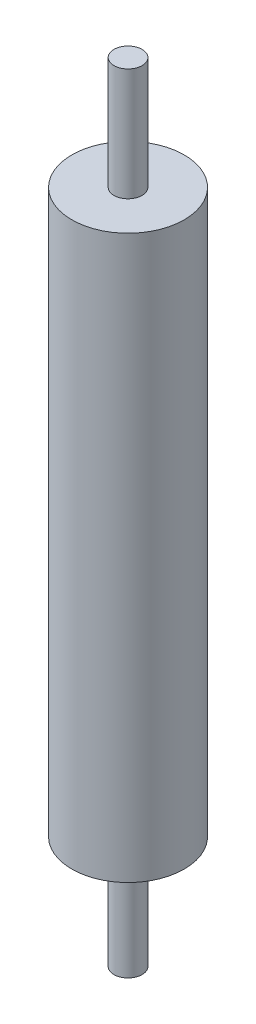
SolidWorks part; units mm, degrees
ref_plane "Front Plane" through (0, 0, 0) normal (0, 0, 1) x (1, 0, 0)
ref_plane "Top Plane" through (0, 0, 0) normal (0, 1, 0) x (1, 0, 0)
ref_plane "Right Plane" through (0, 0, 0) normal (1, 0, 0) x (0, 0, -1)
sketch "Sketch1" plane through (0, 0, 0) normal (0, 0, 1) x (1, 0, 0)
  line L0 (0, 0) -> (-10, 0) construction
  line L1 (0, -70) -> (0, 70) construction
  line L2 (-10, -50) -> (-10, 50)
  line L3 (-10, 50) -> (-2.5, 50)
  line L4 (-2.5, 50) -> (-2.5, 70)
  line L5 (-2.5, 70) -> (0, 70)
  line L6 (-2.5, -70) -> (0, -70)
  line L7 (-2.5, -50) -> (-2.5, -70)
  line L8 (-10, -50) -> (-2.5, -50)
  line L9 (0, -70) -> (0, 70)
  point P6 (0, 73.7927)
  dimension "D1" = 50
  dimension "D2" = 20
  dimension "D3" = 2.5
  dimension "D4" = 10
revolve "Revolve1" add sketch "Sketch1" angle 360 about L9
